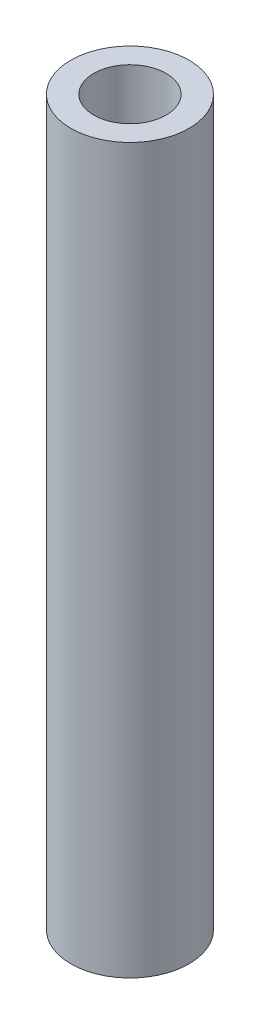
SolidWorks part; units mm, degrees
material "Alliage 1060"
ref_plane "Plan de face" through (0, 0, 0) normal (0, 0, 1) x (1, 0, 0)
ref_plane "Plan de dessus" through (0, 0, 0) normal (0, 1, 0) x (1, 0, 0)
ref_plane "Plan de droite" through (0, 0, 0) normal (1, 0, 0) x (0, 0, -1)
sketch "Esquisse1" plane through (0, 0, 0) normal (0, 1, 0) x (1, 0, 0)
  circle A0 centre (0, 0) radius 1.5
  circle A1 centre (0, 0) radius 2.45
  dimension "D1" = 3
  dimension "D2" = 4.9
extrude "Boss.-Extru.1" add sketch "Esquisse1" along normal blind 30
